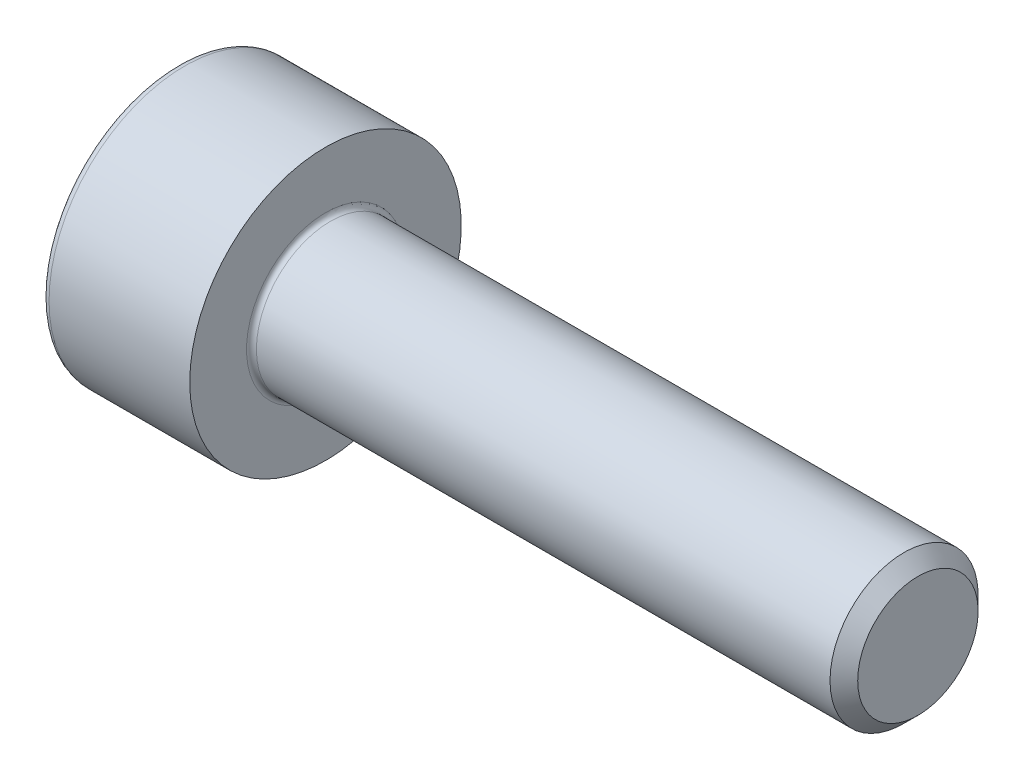
SolidWorks part; units mm, degrees
ref_plane "Plane1" through (0, 0, 0) normal (0, 0, 1) x (1, 0, 0)
ref_plane "Plane2" through (0, 0, 0) normal (0, 1, 0) x (1, 0, 0)
ref_plane "Plane3" through (0, 0, 0) normal (1, 0, 0) x (0, 0, -1)
revolve "Base-Revolve" add sketch "BodySke"
sketch "BodySke" plane through (0, 0, 0) normal (0, 0, 1) x (1, 0, 0)
  line L0 (0, 0) -> (0, 2.75)
  line L1 (0, 2.75) -> (3, 2.75)
  line L2 (3, 2.75) -> (3, 1.5)
  line L3 (3, 1.5) -> (14.7195, 1.5)
  line L4 (15, 1.2195) -> (15, 0)
  line L5 (15, 0) -> (0, 0)
  line L6 (-31.75, 0) -> (127, 0) construction
  line L8 (15, 1.2195) -> (14.7195, 1.5)
  line L10 (15, -1.2195) -> (14.7195, -1.5) construction
  line L11 (3.5, 9.525) -> (3.5, 3.175) construction
  line L12 (3, 9.525) -> (3, 3.175) construction
  line L13 (-45, 9.525) -> (-45, 3.175) construction
  dimension "Diameter" = 3
  dimension "Head_ht" = 3
  dimension "Length" = 12
  dimension "Body_ch_ang" = 45
  dimension "Head_dia" = 5.5
  dimension "Minor_dia" = 2.439
  dimension "Advance" = 0.5
  dimension "Thread_nom" = 12
  dimension "Thread_length" = 60
cosmetic thread "ThreadCosmetic"
fillet "Fillet1" radius 0.1 1 edges at (3, 0, 1.5)
fillet "Fillet2" radius 0.15 1 edges at (0, 0, 2.75)
sketch "Sketch2" plane through (0, 0, 0) normal (0, 0, 1) x (1, 0, 0)
  line L0 (0, 1.28) -> (1.3, 1.28)
  line L1 (1.3, 1.28) -> (2.039, 0)
  line L2 (-31.75, 0) -> (127, 0) construction
  line L3 (2.039, 0) -> (0, 0)
  line L4 (0, 0) -> (0, 1.28)
  line L6 (0, 0) -> (47.625, 0) construction
  dimension "D1" = 1.28
  dimension "D2" = 60
  dimension "Depth" = 1.3
revolve "Hex-PreBroach" cut sketch "Sketch2" angle 360 about L6
sketch "Sketch3" plane through (0, 0, 0) normal (-1, 0, 0) x (0, 0.5, 0.866)
  line L0 (0.739, 1.28) -> (-0.739, 1.28)
  line L1 (-0.739, 1.28) -> (-1.478, 0)
  line L2 (0.739, 1.28) -> (1.478, 0)
  line L3 (0.739, -1.28) -> (1.478, 0)
  line L4 (0.739, -1.28) -> (-0.739, -1.28)
  line L5 (-0.739, -1.28) -> (-1.478, 0)
  dimension "D1" = 1.28
  dimension "D2" = 1.28
  dimension "Hex_size" = 2.56
extrude "Hex" cut sketch "Sketch3" against normal blind 1.3
sketch "ThdSchSke" plane through (0, 0, 0) normal (0, 0, 1) x (1, 0, 0)
  line L0 (4.5, -1.2195) -> (4.3036, -1.5)
  line L1 (4.5, -1.2195) -> (4.6964, -1.5)
  line L2 (4.6964, -1.5) -> (4.6964, -1.875)
  line L3 (-3.175, 0) -> (5.1513, 0) construction
  line L4 (0, 2.6) -> (0, -2.6) construction
  line L5 (4.6964, -1.875) -> (4.3036, -1.875)
  line L6 (4.3036, -1.875) -> (4.3036, -1.5)
  dimension "Thread_minor" = 2.439
  dimension "Diameter" = 3
  dimension "Start" = 4.5
  dimension "SideAngle" = 55
  dimension "VeeAngle" = 70
  dimension "Overcut" = 3.75
revolve "ThreadSchematic" cut sketch "ThdSchSke" angle 360 about L3
pattern_linear "ThdSchPat"
equation "\"D2@Sketch3\" = \"Hex_size@Sketch3\" / 2"
equation "\"D1@Sketch3\" = \"Hex_size@Sketch3\" / 2"
equation "\"D1@Sketch2\" = \"Hex_size@Sketch3\" / 2"
equation "\"Thread_minor@ThreadCosmetic\"  =  \"Minor_dia@BodySke\""
equation "\"Depth@Sketch2\" =  \"Key_eng@Hex\""
equation "\"Thread_length@ThreadCosmetic\" = ((sgn( (\"Length@BodySke\" - \"Advance@BodySke\" * 3.0) - \"Thread_nom@BodySke\" )-1)*( (\"Length@BodySke\" - \"Advance@BodySke\" * 3.0) - \"Thread_nom@BodySke\" ))/-2+ \"Thread_nom@BodySke\""
equation "\"Thread_minor@ThdSchSke\" = \"Minor_dia@BodySke\""
equation "\"Diameter@ThdSchSke\" = \"Diameter@BodySke\""
equation "\"Overcut@ThdSchSke\" = \"Diameter@BodySke\" * 1.25"
equation "\"Start@ThdSchSke\" = \"Head_ht@BodySke\" + \"Length@BodySke\" - \"Thread_length@ThreadCosmetic\"  '---Non-countersunk---"
equation "\"Num_threads@ThdSchPat\" = int( \"Thread_length@ThreadCosmetic\" / \"Advance@BodySke\" + 0.999 )  + 1"
equation "\"Advance@ThdSchPat\" = \"Thread_length@ThreadCosmetic\" /  (\"Num_threads@ThdSchPat\" - 1) 'relax it"
equation "\"Num_threads@ThdSchPat\" = \"Num_threads@ThdSchPat\" - sgn( \"Num_threads@ThdSchPat\" - 1) '---chamfered tips only---"
